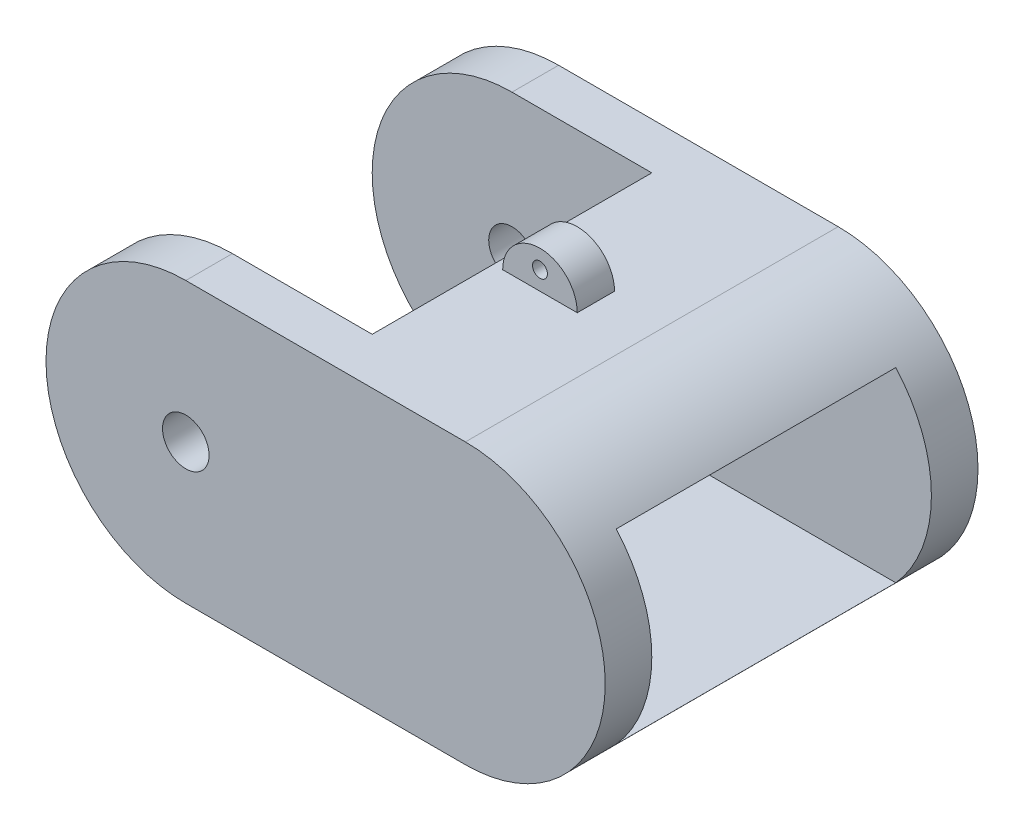
SolidWorks part; units mm, degrees
ref_plane "Front Plane" through (0, 0, 0) normal (0, 0, 1) x (1, 0, 0)
ref_plane "Top Plane" through (0, 0, 0) normal (0, 1, 0) x (1, 0, 0)
ref_plane "Right Plane" through (0, 0, 0) normal (1, 0, 0) x (0, 0, -1)
ref_plane "Right Side Plane" through (0, 0, 12.7) normal (0, 0, 1) x (1, 0, 0)
ref_plane "Inside Plane" through (0, 19.05, 0) normal (0, 1, 0) x (1, 0, 0)
ref_plane "Joint Plane" through (-15.875, 0, 0) normal (1, 0, 0) x (0, 0, -1)
sketch "Sketch1" plane through (0, 0, 0) normal (0, 1, 0) x (1, 0, 0)
  line L1 (-22.225, 12.7) -> (15.875, 12.7)
  line L2 (-22.225, 12.7) -> (-22.225, -12.7)
  line L3 (-22.225, -12.7) -> (15.875, -12.7)
  line L4 (15.875, 12.7) -> (15.875, -12.7)
  dimension "D1" = 38.1
  dimension "D2" = 25.4
  dimension "D3" = 12.7
  dimension "D4" = 15.875
extrude "Boss-Extrude1" add sketch "Sketch1" along normal blind 19.05
sketch "Sketch2" plane through (0, 0, 12.7) normal (0, 0, 1) x (1, 0, 0)
  line L0 (-22.225, 19.05) -> (15.875, 19.05) construction
  line L1 (-22.225, 19.05) -> (-22.225, 0) construction
  line L2 (-22.225, 0) -> (15.875, 0) construction
  line L3 (15.875, 19.05) -> (15.875, 0) construction
  circle A0 centre (-12.7, 9.525) radius 1.5875
  arc A1 (-12.7, 19.05) -> (-12.7, 0) centre (-12.7, 9.525) ccw
  arc A2 (-12.7, 19.05) -> (-12.7, 0) centre (-21.0188, 9.525) ccw
  arc A3 (6.35, 0) -> (6.35, 19.05) centre (6.35, 9.525) ccw
  arc A4 (6.35, 19.05) -> (6.35, 0) centre (13.21, 9.525) cw
extrude "Cut-Extrude2" cut sketch "Sketch2" against normal blind 25.4
sketch "Sketch3" plane through (0, 19.05, 0) normal (0, 1, 0) x (1, 0, 0)
  line L19 (-24.8084, 9.525) -> (-24.8084, -9.525)
  line L26 (6.35, 12.7) -> (-12.7, 12.7) construction
  line L28 (-24.8084, 9.525) -> (-12.7, 9.525)
  line L29 (-12.7, 12.7) -> (-12.7, -12.7) construction
  line L30 (-12.7, 9.525) -> (-12.7, -9.525)
  line L31 (-12.7, -9.525) -> (-24.8084, -9.525)
  line L32 (-12.7, -12.7) -> (6.35, -12.7) construction
  point P0 (-24.8084, 9.1388)
  dimension "D1" = 3.175
  dimension "D2" = 3.175
extrude "Cut-Extrude3" cut sketch "Sketch3" against normal blind 19.05
sketch "Sketch4" plane through (-15.875, 0, 0) normal (1, 0, 0) x (0, 0, -1)
  line L1 (9.525, 15.875) -> (-9.525, 15.875)
  line L2 (9.525, 15.875) -> (9.525, 3.175)
  line L3 (9.525, 3.175) -> (-9.525, 3.175)
  line L4 (-9.525, 15.875) -> (-9.525, 3.175)
  line L6 (7.6835, 19.05) -> (-7.6835, 19.05) construction
  line L10 (9.525, 0) -> (-9.525, 0) construction
  line L12 (-12.7, 19.05) -> (-12.7, 0) construction
  line L13 (12.7, 0) -> (12.7, 19.05) construction
  dimension "D1" = 3.175
  dimension "D2" = 3.175
  dimension "D3" = 3.175
  dimension "D4" = 3.175
extrude "Cut-Extrude4" cut sketch "Sketch4" along normal blind 50.8
sketch "Sketch6" plane through (0, 0, 0) normal (0, 1, 0) x (1, 0, 0)
  line L1 (-6.35, -1.905) -> (1.3106, -1.905)
  line L2 (-6.35, -1.905) -> (-6.35, 1.905)
  line L3 (-6.35, 1.905) -> (1.3106, 1.905)
  line L4 (1.3106, -1.905) -> (1.3106, 1.905)
  line L5 (-12.7, 9.525) -> (-12.7, -9.525) construction
  dimension "D1" = 3.81
  dimension "D2" = 6.35
  dimension "D4" = 1.905
extrude "Boss-Extrude2" add sketch "Sketch6" against normal blind 7.62
sketch "Sketch7" plane through (0, 0, 12.7) normal (0, 0, 1) x (1, 0, 0)
  line L0 (-7.0809, -3.1317) -> (-6.858, 0)
  line L3 (-6.604, 0) -> (-6.604, -7.62) construction
  line L8 (-6.858, 0) -> (-6.858, -7.7678)
  line L9 (-6.858, -7.7678) -> (-14.771, -7.7678)
  line L10 (-14.771, -7.7678) -> (-14.771, 0)
  line L11 (-14.771, 0) -> (-9.975, 0)
  line L12 (1.563, 0) -> (-3.233, 0)
  line L13 (1.563, -7.7678) -> (1.563, 0)
  line L14 (-6.35, -7.7678) -> (1.563, -7.7678)
  line L15 (-6.35, 0) -> (-6.35, -7.7678)
  line L16 (-6.1271, -3.1317) -> (-6.35, 0)
  line L17 (-6.35, -7.62) -> (-6.35, 0) construction
  arc A9 (-8.7944, -2.6143) -> (-9.975, 0) centre (-13.1218, -2.9949) ccw
  arc A10 (-10.1635, -4.3117) -> (-8.7944, -2.6143) centre (-10.9395, -2.285) ccw
  arc A11 (-11.8934, -2.9278) -> (-10.1635, -4.3117) centre (-9.8847, -2.19) ccw
  arc A12 (-10.9962, -2.3329) -> (-11.8934, -2.9278) centre (-11.2469, -2.9288) ccw
  arc A13 (-11.3011, -1.1267) -> (-10.9962, -2.3329) centre (-11.1487, -1.7298) cw
  arc A14 (-13.0445, -2.7718) -> (-11.3011, -1.1267) centre (-11.3965, -2.7719) cw
  arc A15 (-9.5958, -5.7694) -> (-7.0809, -3.1317) centre (-10.0544, -2.8145) ccw
  arc A16 (-13.0445, -2.7718) -> (-9.5958, -5.7694) centre (-10.0544, -2.8145) ccw
  arc A17 (-0.1635, -2.7718) -> (-3.6122, -5.7694) centre (-3.1536, -2.8145) cw
  arc A18 (-3.6122, -5.7694) -> (-6.1271, -3.1317) centre (-3.1536, -2.8145) cw
  arc A19 (-0.1635, -2.7718) -> (-1.9069, -1.1267) centre (-1.8115, -2.7719) ccw
  arc A20 (-1.9069, -1.1267) -> (-2.2118, -2.3329) centre (-2.0593, -1.7298) ccw
  arc A21 (-2.2118, -2.3329) -> (-1.3146, -2.9278) centre (-1.9611, -2.9288) cw
  arc A22 (-1.3146, -2.9278) -> (-3.0445, -4.3117) centre (-3.3233, -2.19) cw
  arc A23 (-3.0445, -4.3117) -> (-4.4136, -2.6143) centre (-2.2685, -2.285) cw
  arc A24 (-4.4136, -2.6143) -> (-3.233, 0) centre (-0.0862, -2.9949) cw
  dimension "D1" = 0.254
  dimension "D2" = 0.254
extrude "Cut-Extrude6" cut sketch "Sketch7" against normal blind 19.05
sketch "Sketch8" plane through (0, 19.05, 0) normal (0, 1, 0) x (1, 0, 0)
  line L1 (-2.54, 1.27) -> (2.54, 1.27)
  line L2 (-2.54, 1.27) -> (-2.54, -1.27)
  line L3 (-2.54, -1.27) -> (2.54, -1.27)
  line L4 (2.54, 1.27) -> (2.54, -1.27)
  dimension "D1" = 2.54
  dimension "D2" = 5.08
  dimension "D3" = 2.54
  dimension "D4" = 1.27
extrude "Boss-Extrude3" add sketch "Sketch8" along normal blind 2.54
sketch "Sketch9" plane through (0, 0, 12.7) normal (0, 0, 1) x (1, 0, 0)
  line L0 (-2.54, 19.05) -> (2.54, 19.05) construction
  line L1 (2.54, 21.59) -> (2.54, 19.05) construction
  line L2 (-2.54, 21.59) -> (2.54, 21.59) construction
  arc A0 (-2.54, 19.05) -> (2.54, 19.05) centre (0, 19.05) cw
  circle A1 centre (0, 20.32) radius 0.508
  arc A2 (-2.54, 19.05) -> (2.54, 19.05) centre (0, 20.4722) cw
  dimension "D1" = 1.27
  dimension "D2" = 2.54
extrude "Cut-Extrude7" cut sketch "Sketch9" against normal blind 19.05
sketch "Sketch10" plane through (0, 19.05, 0) normal (0, 1, 0) x (1, 0, 0)
  line L0 (-12.7, 9.525) -> (-12.7, -9.525) construction
  line L1 (-12.7, 9.525) -> (-3.175, 9.525)
  line L2 (-12.7, 9.525) -> (-12.7, -9.525)
  line L3 (-12.7, -9.525) -> (-3.175, -9.525)
  line L4 (-3.175, 9.525) -> (-3.175, -9.525)
  point P5 (-12.7, -9.525)
  point P8 (-12.7, 9.525)
  dimension "D1" = 9.525
extrude "Cut-Extrude8" cut sketch "Sketch10" against normal blind 3.81
